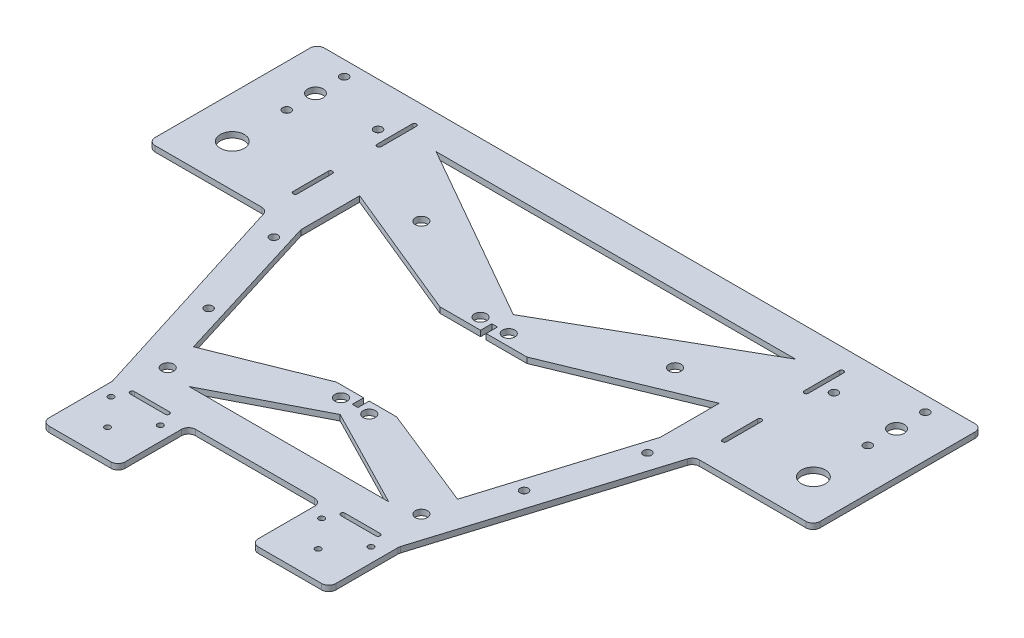
SolidWorks part; units mm, degrees
ref_plane "Front Plane" through (0, 0, 0) normal (0, 0, 1) x (1, 0, 0)
ref_plane "Top Plane" through (0, 0, 0) normal (0, 1, 0) x (1, 0, 0)
ref_plane "Right Plane" through (0, 0, 0) normal (1, 0, 0) x (0, 0, -1)
sketch "Sketch26" plane through (0, 0, 0) normal (0, 1, 0) x (1, 0, 0)
  line L0 (76.0133, 28.8235) -> (76.0133, 88.8235) construction
  line L1 (-63.5382, 76.8235) -> (64.0133, 76.8235)
  line L2 (0.2375, 93.3283) -> (0.2375, -99.0046) construction
  line L3 (21.3527, -51.1765) -> (-20.8776, -51.1765)
  line L4 (76.0133, 88.8235) -> (-76.0328, 88.8235)
  line L5 (-75.5382, 28.8235) -> (-75.5382, 88.8235) construction
  line L6 (115.6892, 88.8235) -> (76.0133, 88.8235)
  line L7 (-77.3734, 28.8235) -> (-115.2142, 28.8235)
  line L8 (-74.9883, 27.0727) -> (-50.5244, -50.8107)
  line L9 (75.4699, 27.0594) -> (51.4834, -50.8168)
  line L10 (-117.7142, 31.3235) -> (-117.7142, 86.3235)
  line L11 (-115.2142, 88.8235) -> (-75.5382, 88.8235)
  line L12 (-75.91, 39.1911) -> (-75.91, 51.6911) construction
  line L13 (-76.66, 39.1911) -> (-76.66, 51.6911)
  line L14 (-75.16, 39.1911) -> (-75.16, 51.6911)
  line L15 (-75.5382, 81.0951) -> (-75.5382, 68.5951) construction
  line L16 (-74.7882, 81.0951) -> (-74.7882, 68.5951)
  line L17 (118.1892, 31.3235) -> (118.1892, 86.3235)
  line L18 (-76.2882, 81.0951) -> (-76.2882, 68.5951)
  line L19 (-46.5978, -26.1765) -> (-10.4569, -11.6765)
  line L20 (77.8592, 28.8235) -> (115.6892, 28.8235)
  line L21 (64.0133, 49.7097) -> (64.0133, 28.8235)
  line L22 (64.0133, 28.8235) -> (47.0729, -26.1765)
  line L23 (-63.5382, 28.8235) -> (-46.5978, -26.1765)
  line L24 (47.0729, -26.1765) -> (10.932, -11.6765)
  line L25 (15.6535, 29.8235) -> (64.0133, 49.7097)
  line L26 (-63.5382, 49.7097) -> (-63.5382, 28.8235)
  line L27 (1.2375, 33.8235) -> (1.2375, 29.8235)
  line L28 (1.2375, 33.8235) -> (-0.7625, 33.8235)
  line L29 (1.2375, 29.8235) -> (15.6535, 29.8235)
  line L30 (-0.7625, 33.8235) -> (-0.7625, 29.8235)
  line L31 (64.0133, 76.8235) -> (0.2375, 40.4366)
  line L32 (-0.7625, 29.8235) -> (-15.1784, 29.8235)
  line L33 (76.0133, 81.0951) -> (76.0133, 68.5951) construction
  line L34 (-15.1784, 29.8235) -> (-63.5382, 49.7097)
  line L35 (-63.5382, 76.8235) -> (0.2375, 40.4366)
  line L36 (1.2375, -11.6765) -> (10.932, -11.6765)
  line L37 (75.2633, 81.0951) -> (75.2633, 68.5951)
  line L38 (1.2375, -15.6765) -> (1.2375, -11.6765)
  line L39 (1.2375, -15.6765) -> (-0.7625, -15.6765)
  line L40 (-0.7625, -15.6765) -> (-0.7625, -11.6765)
  line L41 (-0.7625, -11.6765) -> (-10.4569, -11.6765)
  line L42 (-35.1832, -39.1765) -> (35.6583, -39.1765)
  line L43 (0.2375, -20.9651) -> (35.6583, -39.1765)
  line L44 (0.2375, -20.9651) -> (-35.1832, -39.1765)
  line L45 (51.3727, -51.5527) -> (51.3727, -73.6765)
  line L46 (48.8727, -76.1765) -> (26.3527, -76.1765)
  line L47 (76.7633, 81.0951) -> (76.7633, 68.5951)
  line L48 (76.3851, 39.1911) -> (76.3851, 51.6911) construction
  line L49 (77.1351, 39.1911) -> (77.1351, 51.6911)
  line L50 (75.6351, 39.1911) -> (75.6351, 51.6911)
  line L51 (23.8527, -73.6765) -> (23.8527, -53.6765)
  line L52 (37.6127, -76.1765) -> (37.6127, -51.1765) construction
  line L53 (51.3727, -76.1765) -> (51.3727, -51.1765)
  line L54 (23.8527, -51.1765) -> (23.8527, -76.1765)
  line L55 (-50.4095, -51.5599) -> (-50.4095, -73.6765)
  line L56 (-47.9095, -76.1765) -> (-25.8776, -76.1765)
  line L57 (-23.3776, -73.6765) -> (-23.3776, -53.6765)
  line L58 (31.3532, -51.1727) -> (43.8532, -51.1727) construction
  line L59 (31.3532, -50.4227) -> (43.8532, -50.4227)
  line L60 (31.3532, -51.9227) -> (43.8532, -51.9227)
  line L61 (-30.8781, -51.1727) -> (-43.3781, -51.1727) construction
  line L62 (-30.8781, -50.4227) -> (-43.3781, -50.4227)
  line L63 (-30.8781, -51.9227) -> (-43.3781, -51.9227)
  circle A0 centre (45.2375, 52.8235) radius 2.15
  circle A1 centre (45.2375, -37.1765) radius 2.15
  circle A2 centre (5.2375, 33.8235) radius 2.15
  circle A3 centre (5.2375, -15.6765) radius 2.15
  circle A4 centre (103.3133, 43.8235) radius 4.25
  arc A5 (118.1892, 31.3235) -> (115.6892, 28.8235) centre (115.6892, 31.3235) cw
  circle A6 centre (103.3133, 73.3235) radius 2.75
  circle A7 centre (103.3133, 83.5235) radius 1.45
  circle A8 centre (103.3133, 63.1235) radius 1.45
  circle A9 centre (81.1133, 73.3235) radius 1.45
  arc A10 (118.1892, 86.3235) -> (115.6892, 88.8235) centre (115.6892, 86.3235) ccw
  arc A11 (-117.7142, 86.3235) -> (-115.2142, 88.8235) centre (-115.2142, 86.3235) cw
  circle A12 centre (-80.6382, 73.3235) radius 1.45
  circle A13 centre (-102.8382, 63.1235) radius 1.45
  circle A14 centre (-102.8382, 83.5235) radius 1.45
  circle A15 centre (-102.8382, 73.3235) radius 2.75
  arc A16 (-117.7142, 31.3235) -> (-115.2142, 28.8235) centre (-115.2142, 31.3235) ccw
  arc A17 (75.2633, 81.0951) -> (76.7633, 81.0951) centre (76.0133, 81.0951) cw
  circle A18 centre (-102.8382, 43.8235) radius 4.25
  circle A19 centre (-4.7625, -15.6765) radius 2.15
  arc A20 (76.7633, 68.5951) -> (75.2633, 68.5951) centre (76.0133, 68.5951) cw
  arc A21 (77.1351, 39.1911) -> (75.6351, 39.1911) centre (76.3851, 39.1911) cw
  arc A22 (75.6351, 51.6911) -> (77.1351, 51.6911) centre (76.3851, 51.6911) cw
  circle A23 centre (-4.7625, 33.8235) radius 2.15
  circle A24 centre (-44.7625, -37.1765) radius 2.15
  circle A25 centre (-44.7625, 52.8235) radius 2.15
  arc A26 (-76.66, 39.1911) -> (-75.16, 39.1911) centre (-75.91, 39.1911) ccw
  arc A27 (-75.16, 51.6911) -> (-76.66, 51.6911) centre (-75.91, 51.6911) ccw
  arc A28 (-74.7882, 81.0951) -> (-76.2882, 81.0951) centre (-75.5382, 81.0951) ccw
  arc A29 (-76.2882, 68.5951) -> (-74.7882, 68.5951) centre (-75.5382, 68.5951) ccw
  circle A30 centre (28.8527, -56.1765) radius 1
  circle A31 centre (37.6127, -66.1765) radius 1
  circle A32 centre (46.3727, -56.1765) radius 1
  circle A33 centre (28.8527, -56.1765) radius 1
  circle A34 centre (46.3727, -56.1765) radius 1
  circle A35 centre (-28.3776, -56.1765) radius 1
  circle A36 centre (-45.8976, -56.1765) radius 1
  circle A37 centre (-37.1376, -66.1765) radius 1
  arc A38 (31.3532, -50.4227) -> (31.3532, -51.9227) centre (31.3532, -51.1727) ccw
  arc A39 (43.8532, -51.9227) -> (43.8532, -50.4227) centre (43.8532, -51.1727) ccw
  arc A40 (-30.8781, -50.4227) -> (-30.8781, -51.9227) centre (-30.8781, -51.1727) cw
  arc A41 (-43.3781, -51.9227) -> (-43.3781, -50.4227) centre (-43.3781, -51.1727) cw
  arc A42 (77.8592, 28.8235) -> (75.4699, 27.0594) centre (77.8592, 26.3235) ccw
  arc A43 (-74.9883, 27.0727) -> (-77.3734, 28.8235) centre (-77.3734, 26.3235) ccw
  arc A44 (51.3727, -51.5527) -> (51.4834, -50.8168) centre (53.8727, -51.5527) cw
  arc A45 (21.3527, -51.1765) -> (23.8527, -53.6765) centre (21.3527, -53.6765) cw
  arc A46 (-20.8776, -51.1765) -> (-23.3776, -53.6765) centre (-20.8776, -53.6765) ccw
  arc A47 (-50.4095, -51.5599) -> (-50.5244, -50.8107) centre (-52.9095, -51.5599) ccw
  arc A48 (-23.3776, -73.6765) -> (-25.8776, -76.1765) centre (-25.8776, -73.6765) cw
  arc A49 (-47.9095, -76.1765) -> (-50.4095, -73.6765) centre (-47.9095, -73.6765) cw
  circle A50 centre (66.5105, 21.7513) radius 1.45
  circle A51 centre (56.2078, -11.698) radius 1.45
  circle A52 centre (-55.7328, -11.698) radius 1.45
  circle A53 centre (-66.0354, 21.7513) radius 1.45
  arc A54 (48.8727, -76.1765) -> (51.3727, -73.6765) centre (48.8727, -73.6765) ccw
  arc A55 (26.3527, -76.1765) -> (23.8527, -73.6765) centre (26.3527, -73.6765) cw
  point P60 (-75.91, 45.4411)
  point P63 (76.0133, 74.8451)
  point P71 (76.3851, 45.4411)
  point P77 (-75.5382, 74.8451)
  point P99 (0.2375, 33.8235)
  point P107 (0.2375, -15.6765)
  point P112 (0.2375, -39.1765)
  point P136 (37.6032, -51.1727)
  point P143 (-37.1281, -51.1727)
  point P162 (-23.3776, -51.1765)
  point P167 (-23.3776, -76.1765)
  dimension "D6" = 4.3
  dimension "D13" = 8.5
  dimension "D14" = 2.9
  dimension "D15" = 2.9
  dimension "D16" = 2.9
  dimension "D10" = 2.5
  dimension "D21" = 2.5
  dimension "D3" = 45
  dimension "D7" = 4.3
  dimension "D8" = 5.5
  dimension "D22" = 19
  dimension "D4" = 49.5
  dimension "D11" = 4.3
  dimension "D24" = 4.3
  dimension "D28" = 5
  dimension "D36" = 15
  dimension "D37" = 2.5
  dimension "D38" = 2.9
  dimension "D41" = 2.9
  dimension "D40" = 2.5
  dimension "D5" = 90
  dimension "D12" = 15
  dimension "D17" = 10.2
  dimension "D18" = 10.2
  dimension "D19" = 22.2
  dimension "D20" = 29.5
  dimension "D9" = 40
  dimension "D23" = 40
  dimension "D25" = 36
  dimension "D26" = 45
  dimension "D27" = 12
  dimension "D29" = 12
  dimension "D30" = 12
  dimension "D31" = 1
  dimension "D32" = 4
  dimension "D33" = 27.52
  dimension "D34" = 25
  dimension "D35" = 5
  dimension "D39" = 7
  dimension "D42" = 35
extrude "Boss-Extrude4" add sketch "Sketch26" along normal blind 2
